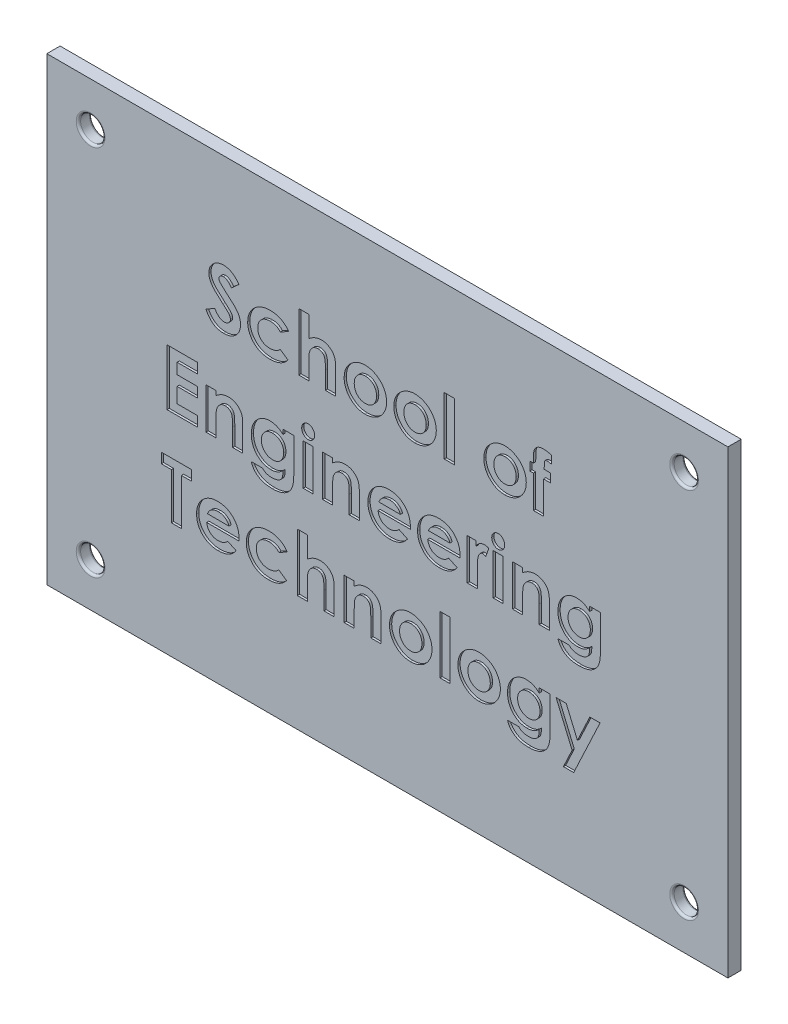
SolidWorks part; units mm, degrees
ref_plane "Front Plane" through (0, 0, 0) normal (0, 0, 1) x (1, 0, 0)
ref_plane "Top Plane" through (0, 0, 0) normal (0, 1, 0) x (1, 0, 0)
ref_plane "Right Plane" through (0, 0, 0) normal (1, 0, 0) x (0, 0, -1)
sketch "Sketch1" plane through (0, 0, 0) normal (0, 0, 1) x (1, 0, 0)
  line L1 (-77.025, -52.02) -> (77.025, -52.02)
  line L2 (-77.025, -52.02) -> (-77.025, 52.02)
  line L3 (-77.025, 52.02) -> (77.025, 52.02)
  line L4 (77.025, -52.02) -> (77.025, 52.02)
  line L5 (-77.025, -52.02) -> (77.025, 52.02) construction
  line L6 (-77.025, 52.02) -> (77.025, -52.02) construction
  point P0 (0, 0)
  dimension "D1" = 154.05
  dimension "D2" = 104.04
extrude "Boss-Extrude1" add sketch "Sketch1" along normal blind 3
sketch "Sketch2" plane through (0, 0, 3) normal (0, 0, 1) x (1, 0, 0)
  line L0 (77.025, 52.02) -> (-77.025, 52.02) construction
  line L1 (-77.025, 52.02) -> (-77.025, -52.02) construction
  line L2 (0, 0) -> (0, 50000) construction
  line L3 (0, 0) -> (50000, 0) construction
  circle A0 centre (-67.125, 42.12) radius 2.75
  circle A1 centre (67.125, 42.12) radius 2.75
  circle A2 centre (67.125, -42.12) radius 2.75
  circle A3 centre (-67.125, -42.12) radius 2.75
  dimension "D1" = 9.9
  dimension "D3" = 5.5
  dimension "D2" = 9.9
extrude "Cut-Extrude1" cut sketch "Sketch2" against normal through all
sketch "Sketch3" plane through (0, 0, 3) normal (0, 0, 1) x (1, 0, 0)
  text T1 "<b>  School of </b>\r\n<b>Engineering</b>\r\n<b>Technology</b>" font "Century Gothic" height in points 48
extrude "Cut-Extrude2" cut sketch "Sketch3" against normal blind 0.5
sketch "Sketch5" [suppressed] plane through (0, 0, 3) normal (0, 0, 1) x (1, 0, 0)
  line L0 (-9.7309, 10.0231) -> (-15.5666, -6.0101)
  line L1 (-15.5666, -6.0101) -> (-22.7346, -6.0101)
  line L2 (-22.7346, -6.0101) -> (-25.4708, -13.5277)
  line L3 (-25.4708, -13.5277) -> (-1.3321, -13.5277)
  line L4 (-1.3321, -13.5277) -> (1.4041, -6.0101)
  line L5 (1.4041, -6.0101) -> (-2.2976, -6.0101)
  line L6 (-2.2976, -6.0101) -> (-1.2716, -3.1911)
  line L7 (-1.2716, -3.1911) -> (15.0107, -3.1911)
  line L8 (-11.7357, 17.5407) -> (15.0107, 17.5407)
  line L9 (-16.899, 10.0231) -> (-9.7309, 10.0231)
  line L10 (-16.899, 10.0231) -> (-14.1628, 17.5407)
  line L11 (-14.1628, 17.5407) -> (-11.7357, 17.5407)
  line L12 (1.8173, 5.2954) -> (3.1853, 9.0542)
  line L13 (3.1853, 9.0542) -> (15.0107, 9.0542)
  line L14 (1.8173, 5.2954) -> (15.0107, 5.2954)
  line L15 (-12.5872, 8.0231) -> (-16.967, -4.0101)
  line L16 (-16.967, -4.0101) -> (-24.1351, -4.0101)
  line L17 (-24.1351, -4.0101) -> (-28.3271, -15.5277)
  line L18 (-28.3271, -15.5277) -> (0.0683, -15.5277)
  line L19 (-11.7357, 19.5407) -> (15.0107, 19.5407)
  line L20 (-15.5633, 19.5407) -> (-11.7357, 19.5407)
  line L21 (-19.7553, 8.0231) -> (-15.5633, 19.5407)
  line L22 (-19.7553, 8.0231) -> (-12.5872, 8.0231)
  line L24 (0.0683, -15.5277) -> (3.8305, -5.1911)
  line L26 (3.8305, -5.1911) -> (15.0107, -5.1911)
  arc A0 (15.0107, 17.5407) -> (15.0107, -3.1911) centre (15.0107, 7.1748) cw
  arc A1 (15.0107, 9.0542) -> (15.0107, 5.2954) centre (15.0107, 7.1748) cw
  arc A2 (15.0107, 19.5407) -> (15.0107, -5.1911) centre (15.0107, 7.1748) cw
  point P2 (2.5013, 7.1748)
  dimension "D1" = 3
  dimension "D2" = 4
extrude "Cut-Extrude4" [suppressed] cut sketch "Sketch5" against normal blind 0.5 contours A1 L13 L12 L14 | A2 L19 L20 L21 L22 L15 L16 L17 L18 L24 L26 L8 A0 L7 L6 L5 L4 L3 L2 L1 L0 L9 L10 L11
sketch "Sketch7" [suppressed] plane through (0, 0, 3) normal (0, 0, 1) x (1, 0, 0)
  line L6 (-30.4289, 18.0795) -> (-30.4289, -17.8005)
  line L9 (29.5711, 18.0795) -> (-30.4289, 18.0795)
  line L10 (29.7809, 15.3195) -> (-3.3534, 15.3195)
  line L12 (29.5711, 18.0795) -> (29.5711, -17.8005)
  line L13 (29.7809, 12.5595) -> (-3.3534, 12.5595)
  line L14 (29.7809, 9.7995) -> (-3.3534, 9.7995)
  line L16 (29.7809, 7.0395) -> (-3.3534, 7.0395)
  line L580 (29.7809, 4.2795) -> (-3.3534, 4.2795)
  line L581 (29.7809, 1.5195) -> (-3.3534, 1.5195)
  line L582 (29.5711, -1.2405) -> (-30.4289, -1.2405)
  line L584 (29.5711, -4.0005) -> (-30.4289, -4.0005)
  line L1148 (29.5711, -6.7605) -> (-30.4289, -6.7605)
  line L1149 (29.5711, -9.5205) -> (-30.4289, -9.5205)
  line L1150 (29.5711, -12.2805) -> (-30.4289, -12.2805)
  line L1151 (-30.4289, -1.2405) -> (-30.4289, 18.0795)
  line L1152 (29.5711, -15.0405) -> (-30.4289, -15.0405)
  line L1153 (29.5711, -17.8005) -> (-30.4289, -17.8005)
  line L1154 (-30.4289, -1.2405) -> (-4.3534, -1.2405)
  line L1155 (-4.3534, 1.5195) -> (-4.3534, 4.2795)
  line L1156 (-30.4289, 18.0795) -> (-4.3534, 18.0795)
  line L1729 (-4.3534, 12.5595) -> (-4.3534, 15.3195)
  line L1730 (-4.3534, 7.0395) -> (-4.3534, 9.7995)
  line L1731 (-4.3534, 18.0795) -> (-4.3534, -1.2405)
  line L1732 (-3.3534, 18.0795) -> (-3.3534, -1.2405)
  dimension "D1" = 1
extrude "Cut-Extrude7" [suppressed] cut sketch "Sketch7" against normal blind 0.5
sketch "Sketch8" [suppressed] plane through (0, 0, 3) normal (0, 0, 1) x (1, 0, 0)
  text T0 "<b>    Purdue</b>\r\n<b>Polytechnic</b>\r\n<b>    Institute</b>" font "Century Gothic" height in points 48
extrude "Cut-Extrude8" [suppressed] cut sketch "Sketch8" against normal blind 0.5
fillet "Fillet1" radius 0.5 8 edges at (64.375, 42.12, 3) (64.375, 42.12, 0) (69.875, -42.12, 3) (69.875, -42.12, 0) (-69.875, -42.12, 3) (-69.875, -42.12, 0) (-64.375, 42.12, 3) (-64.375, 42.12, 0)
